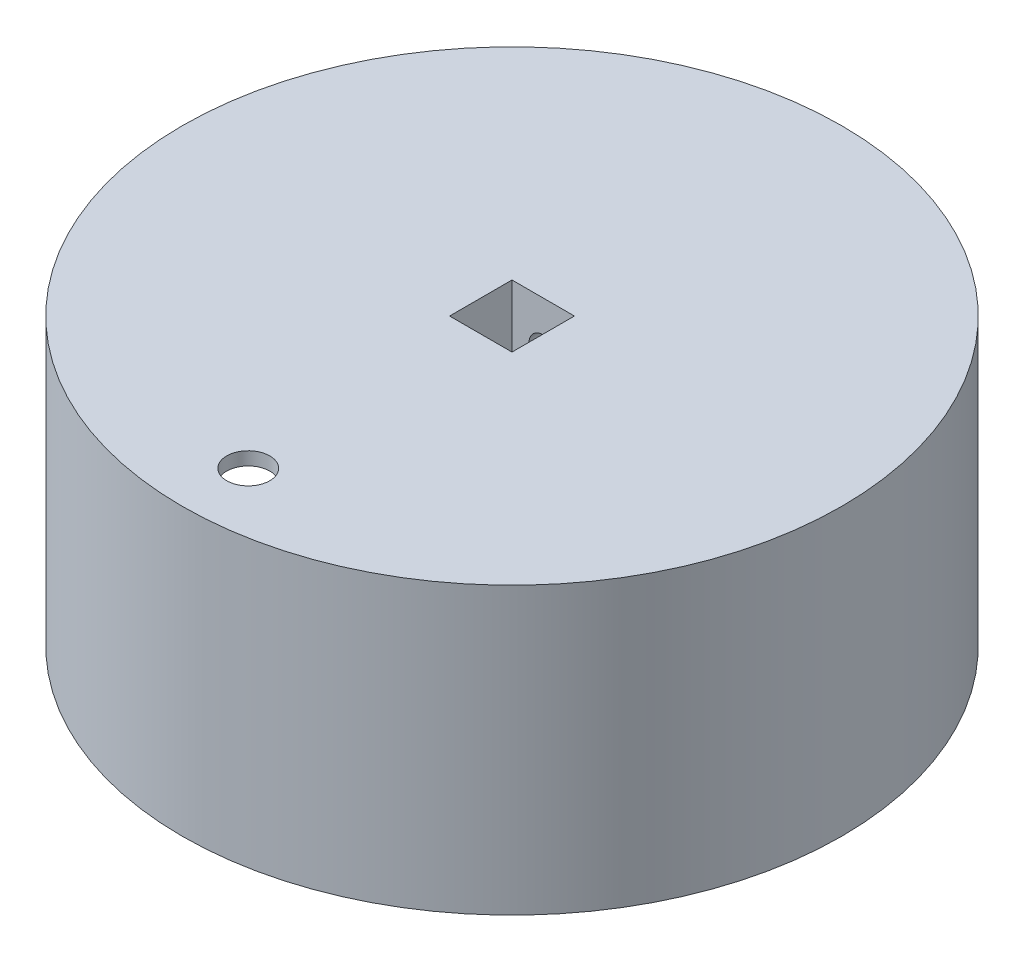
SolidWorks part; units mm, degrees
ref_plane "Front" through (0, 0, 0) normal (0, 0, 1) x (1, 0, 0)
ref_plane "Top" through (0, 0, 0) normal (0, 1, 0) x (1, 0, 0)
ref_plane "Right" through (0, 0, 0) normal (1, 0, 0) x (0, 0, -1)
sketch "Sketch1" plane through (0, 0, 0) normal (0, 1, 0) x (1, 0, 0)
  circle A0 centre (0, 0) radius 75
  dimension "D1" = 150
extrude "Boss-Extrude1" add sketch "Sketch1" along normal blind 65
chamfer "Chamfer1" [suppressed] distance 10 angle 45
shell "Shell1" thickness 3
sketch "Sketch2" plane through (0, 65, 0) normal (0, 1, 0) x (1, 0, 0)
  line L1 (-7.1, 7.1) -> (7.1, 7.1)
  line L2 (-7.1, 7.1) -> (-7.1, -7.1)
  line L3 (-7.1, -7.1) -> (7.1, -7.1)
  line L4 (7.1, 7.1) -> (7.1, -7.1)
  line L5 (-7.1, 7.1) -> (7.1, -7.1) construction
  line L6 (-7.1, -7.1) -> (7.1, 7.1) construction
  point P0 (0, 0)
  dimension "D1" = 14.2
extrude "Cut-Extrude1" cut sketch "Sketch2" against normal through all
sketch "Sketch3" plane through (0, 62, 0) normal (0, -1, 0) x (1, 0, 0)
  line L0 (-7.1, 7.1) -> (-7.1, -7.1)
  line L1 (-7.1, -7.1) -> (7.1, -7.1)
  line L2 (7.1, -7.1) -> (7.1, 7.1)
  line L3 (7.1, 7.1) -> (12.1, 7.1)
  line L4 (12.1, 7.1) -> (12.1, -12.1)
  line L5 (12.1, -12.1) -> (-12.1, -12.1)
  line L6 (-12.1, -12.1) -> (-12.1, 7.1)
  line L7 (-12.1, 7.1) -> (-7.1, 7.1)
  point P4 (0, -12.1)
  dimension "D1" = 5
  dimension "D2" = 5
extrude "Boss-Extrude2" add sketch "Sketch3" along normal offset from surface (59 mm away) 3 up to face at (0, 0, 72)
chamfer "Chamfer2" distance 10 angle 45 5 edges at (12.1, 62, -2.5) (0, 62, -12.1) (-12.1, 62, -2.5) (-9.6, 62, 7.1) (9.6, 62, 7.1)
sketch "Sketch14" plane through (0, 3, 0) normal (0, -1, 0) x (1, 0, 0)
  line L0 (12.1, -12.1) -> (-12.1, -12.1) construction
  line L1 (-9, -12.1) -> (9, -12.1)
  line L2 (-9, -12.1) -> (-9, -22.1)
  line L3 (-9, -22.1) -> (9, -22.1)
  line L4 (9, -12.1) -> (9, -22.1)
  line L5 (22.1, -22.1) -> (-22.1, -22.1) construction
  point P8 (0, -22.1)
  dimension "D1" = 18
extrude "Cut-Extrude7" cut sketch "Sketch14" against normal up to surface (59 mm away) up to face at (0, 62, 72)
sketch "Sketch5" plane through (0, 3, 0) normal (0, -1, 0) x (1, 0, 0)
  line L1 (-12.1, 7.1) -> (12.1, 7.1)
  line L2 (-12.1, 7.1) -> (-12.1, -12.1)
  line L3 (-12.1, -12.1) -> (12.1, -12.1)
  line L4 (12.1, 7.1) -> (12.1, -12.1)
extrude "Boss-Extrude3" add sketch "Sketch5" against normal blind 5
sketch "Sketch6" plane through (0, 0, -7.1) normal (0, 0, 1) x (1, 0, 0)
  line L0 (7.1, 8) -> (-7.1, 8) construction
  circle A0 centre (0, 54.5) radius 3.25
  circle A1 centre (0, 19.5) radius 3.25
  dimension "D1" = 6.5
  dimension "D2" = 35
  dimension "D3" = 11.5
extrude "Cut-Extrude2" cut sketch "Sketch6" against normal up to next
sketch "Sketch12" plane through (0, 0, 0) normal (0, -1, 0) x (1, 0, 0)
  line L0 (-10, -71.3022) -> (10, -71.3022)
  circle A0 centre (0, 0) radius 72 construction
  arc A1 (-10, -71.3022) -> (10, -71.3022) centre (0, 0) ccw
  point P5 (0, -71.3022)
  dimension "D1" = 20
extrude "Boss-Extrude5" add sketch "Sketch12" against normal up to next
sketch "Sketch7" plane through (0, 0, -12.1) normal (0, 0, 1) x (1, 0, 0)
  line L0 (-5.25, 14.9047) -> (-5.25, 9.0953)
  line L1 (0, 12) -> (0, 0) construction
  line L2 (-75, 0) -> (75, 0) construction
  line L3 (5.25, 14.9047) -> (5.25, 9.0953)
  line L4 (75, 65) -> (-75, 65) construction
  line L5 (3, 59.8) -> (-3, 59.8)
  line L6 (6, 56.8) -> (6, 54.8)
  line L7 (3, 51.8) -> (-3, 51.8)
  line L8 (-6, 56.8) -> (-6, 54.8)
  line L9 (6, 59.8) -> (-6, 51.8) construction
  line L10 (6, 51.8) -> (-6, 59.8) construction
  arc A0 (-5.25, 9.0953) -> (5.25, 9.0953) centre (0, 12) ccw
  arc A1 (5.25, 14.9047) -> (-5.25, 14.9047) centre (0, 12) ccw
  arc A2 (6, 54.8) -> (3, 51.8) centre (3, 54.8) cw
  arc A3 (3, 59.8) -> (6, 56.8) centre (3, 56.8) cw
  arc A4 (-3, 59.8) -> (-6, 56.8) centre (-3, 56.8) ccw
  arc A5 (-3, 51.8) -> (-6, 54.8) centre (-3, 54.8) cw
  point P1 (0, 55.8)
  dimension "D1" = 12
  dimension "D7" = 3
  dimension "D2" = 12
  dimension "D3" = 10.5
  dimension "D4" = 12
  dimension "D5" = 8
  dimension "D6" = 9.2
extrude "Virransyöttö ja USB" cut sketch "Sketch7" against normal up to surface (62.716 mm away)
sketch "Sketch8" plane through (0, 62, 0) normal (0, -1, 0) x (1, 0, 0)
  line L0 (0, 0) -> (48.0833, 48.0833) construction
  line L1 (-12.1, 7.1) -> (12.1, 7.1) construction
  circle A0 centre (0, 0) radius 72 construction
  arc A1 (54.9164, 46.5639) -> (46.5639, 54.9164) centre (0, 0) ccw
  arc A2 (46.5639, 54.9164) -> (54.9164, 46.5639) centre (48.0833, 48.0833) ccw
  dimension "D1" = 135
  dimension "D2" = 7
  dimension "D3" = 4
extrude "Boss-Extrude4" add sketch "Sketch8" along normal offset from surface (59 mm away) 3 up to face at (0, 0, 0.3489)
fillet "Fillet1" radius 3 2 edges at (54.9164, 32.5, 46.5639) (46.5639, 32.5, 54.9164)
sketch "Sketch9" plane through (0, 3, 0) normal (0, -1, 0) x (1, 0, 0)
  line L0 (0, 0) -> (45.9619, 45.9619) construction
  circle A0 centre (45.9619, 45.9619) radius 1.25
  arc A3 (43.27, 53.1658) -> (53.1658, 43.27) centre (48.0833, 48.0833) ccw construction
  point P6 (43.1335, 43.1335)
  dimension "D1" = 2.5
  dimension "D2" = 65
extrude "Cut-Extrude4" cut sketch "Sketch9" against normal blind 15
pattern_circular "CirPattern1" count 4 over 360 about axis through (0, 0, 0) along (0, 1, 0) of "Boss-Extrude4", "Fillet1", "Cut-Extrude4"
sketch "Sketch10" plane through (0, 62, 0) normal (0, -1, 0) x (1, 0, 0)
  circle A0 centre (0, 60) radius 4.9
  dimension "D1" = 9.8
  dimension "D2" = 60
extrude "Mikrofoni" cut sketch "Sketch10" against normal through all
sketch "Sketch11" plane through (0, 3, 0) normal (0, -1, 0) x (1, 0, 0)
  circle A0 centre (0, 0) radius 1.25
  dimension "D1" = 2.5
extrude "Cut-Extrude6" cut sketch "Sketch11" against normal blind 15
sketch "Sketch13" plane through (0, 62, 0) normal (0, -1, 0) x (1, 0, 0)
  line L0 (-10.605, -39.8022) -> (8.845, -68.3022) construction
  line L1 (10, -71.3022) -> (-10, -71.3022) construction
  line L2 (0, 0) -> (0, 60) construction
  circle A0 centre (-10.605, -39.8022) radius 0.75
  circle A1 centre (8.845, -68.3022) radius 0.75
  circle A2 centre (8.845, -68.3022) radius 3.5
  circle A3 centre (-10.605, -39.8022) radius 3.5
  circle A4 centre (-7.43, 33.25) radius 3.5
  circle A5 centre (-7.43, 33.25) radius 0.75
  circle A6 centre (7.43, 33.25) radius 0.75
  circle A7 centre (7.43, 33.25) radius 3.5
  circle A8 centre (0, 60) radius 4.9 construction
  point P6 (-0.88, -54.0522)
  dimension "D1" = 19.45
  dimension "D2" = 28.5
  dimension "D3" = 1.5
  dimension "D4" = 7
  dimension "D7" = 14.86
  dimension "D8" = 26.75
  dimension "D5" = 0.88
  dimension "D6" = 3
extrude "Boss-Extrude6" add sketch "Sketch13" along normal blind 4
chamfer "Chamfer3" distance 1 angle 45 4 edges at (8.7321, 62, -64.804) (-10.605, 62, -36.3022) (-7.43, 62, 36.75) (7.43, 62, 36.75)
